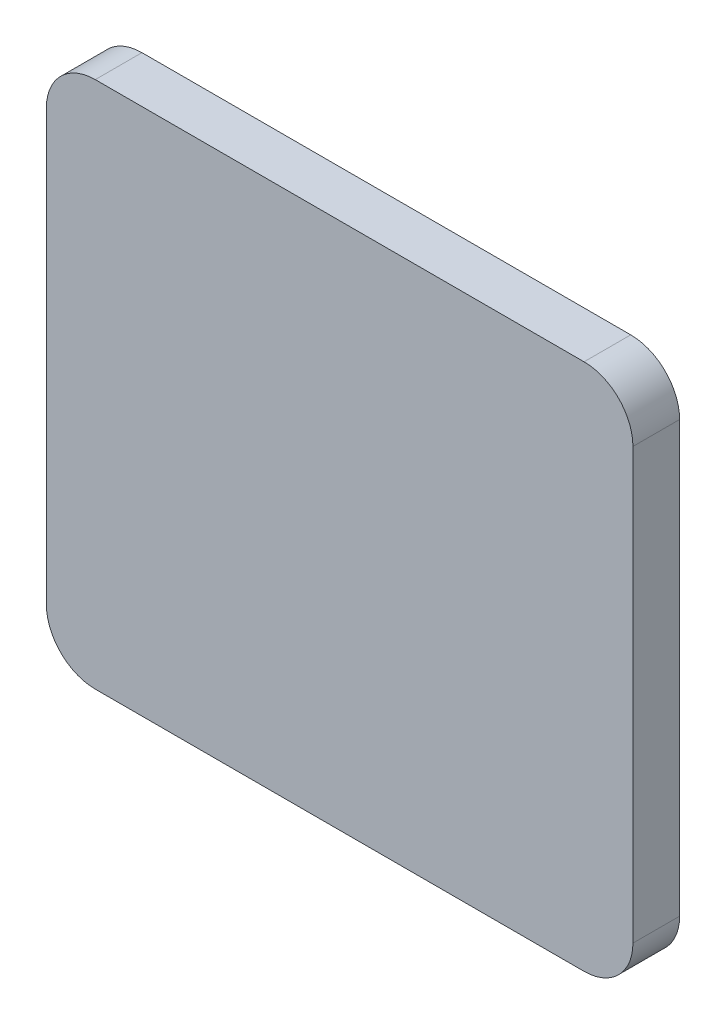
SolidWorks part; units mm, degrees
ref_plane "Front Plane" through (0, 0, 0) normal (0, 0, 1) x (1, 0, 0)
ref_plane "Top Plane" through (0, 0, 0) normal (0, 1, 0) x (1, 0, 0)
ref_plane "Right Plane" through (0, 0, 0) normal (1, 0, 0) x (0, 0, -1)
sketch "Sketch1" plane through (0, 0, 0) normal (0, 0, 1) x (1, 0, 0)
  line L0 (0, 5) -> (0, 49)
  line L1 (5, 0) -> (55, 0)
  line L2 (5, 54) -> (55, 54)
  line L3 (60, 49) -> (60, 5)
  arc A0 (0, 49) -> (5, 54) centre (5, 49) cw
  arc A1 (0, 5) -> (5, 0) centre (5, 5) ccw
  arc A2 (55, 0) -> (60, 5) centre (55, 5) ccw
  arc A3 (55, 54) -> (60, 49) centre (55, 49) cw
  point P7 (0, 54)
  point P10 (0, 0)
  point P13 (60, 0)
  dimension "D3" = 5
  dimension "D4" = 5
  dimension "D1" = 54
  dimension "D2" = 60
extrude "Boss-Extrude1" add sketch "Sketch1" along normal blind 4.7752
sketch "Sketch2" plane through (0, 0, 4.7752) normal (0, 0, 1) x (1, 0, 0)
  line L0 (183.0186, 521.1891) -> (865.6852, 521.1891) construction
  line L1 (183.4721, 529.4822) -> (866.1387, 529.4822) construction
  line L2 (181.2439, 528.0548) -> (863.9106, 528.0548) construction
  line L7 (19.8691, 28.8438) -> (19.2881, 28.3572)
  line L8 (19.2881, 28.3572) -> (18.8822, 27.9078)
  line L9 (18.8822, 27.9078) -> (18.3075, 27.2715)
  line L10 (18.3075, 27.2715) -> (17.8606, 26.7766)
  line L11 (17.8606, 26.7766) -> (17.5763, 26.4618)
  line L12 (17.5763, 26.4618) -> (17.4224, 26.2372)
  line L13 (17.4224, 26.2372) -> (17.2492, 25.9065)
  line L14 (17.2492, 25.9065) -> (17.2492, 25.6606)
  line L15 (17.2492, 25.6606) -> (17.2492, 25.3807)
  line L16 (17.2492, 25.3807) -> (17.4224, 24.2786)
  line L17 (17.4224, 24.2786) -> (17.6828, 23.5807)
  line L18 (17.6828, 23.5807) -> (17.8362, 23.1695)
  line L19 (17.8362, 23.1695) -> (17.9803, 22.7832)
  line L20 (17.9803, 22.7832) -> (18.1007, 22.4604)
  line L21 (18.1007, 22.4604) -> (18.2144, 22.1557)
  line L22 (18.4085, 20.4831) -> (17.7442, 19.7163)
  line L23 (21.1826, 20.9352) -> (21.7477, 18.6362)
  line L24 (30.0623, 41.0301) -> (30.3939, 40.8005)
  line L25 (30.3939, 40.8005) -> (30.5707, 40.8005)
  line L26 (30.5707, 40.8005) -> (30.7622, 40.9153)
  line L27 (38.1812, 40.4733) -> (38.4921, 39.9546)
  line L28 (38.0447, 39.328) -> (38.0816, 39.0467)
  line L29 (36.2955, 38.0196) -> (36.6942, 37.6823)
  line L30 (37.0925, 36.8802) -> (37.8941, 35.8611)
  line L31 (38.6385, 35.2424) -> (39.1212, 35.283)
  line L32 (39.1212, 35.283) -> (40.0166, 36.0841)
  line L33 (40.0166, 36.0841) -> (40.7211, 36.9169)
  line L34 (42.8215, 41.0301) -> (43.2748, 41.9093)
  line L35 (43.2748, 41.9093) -> (43.1854, 41.9728)
  line L36 (43.1854, 41.9728) -> (44.4975, 43.2915)
  line L37 (44.4975, 43.2915) -> (44.3554, 42.3659)
  line L38 (44.3554, 42.3659) -> (44.2137, 41.4319)
  line L39 (44.2137, 41.4319) -> (44.1203, 41.4319)
  line L40 (44.1203, 41.4319) -> (43.5539, 40.2139)
  line L41 (43.21, 37.2316) -> (43.21, 36.9573)
  line L42 (43.257, 36.7903) -> (43.257, 36.4775)
  line L43 (42.7089, 35.7793) -> (42.7089, 35.2023)
  line L44 (40.0908, 30.5826) -> (40.0908, 28.8438)
  line L45 (40.0908, 28.8438) -> (40.0908, 28.3572)
  line L46 (40.0908, 28.3572) -> (42.0558, 26.1361)
  line L47 (42.0558, 26.1361) -> (42.3352, 25.8202)
  line L48 (42.6677, 24.2006) -> (42.9387, 23.1123)
  line L49 (42.9387, 23.1123) -> (43.3368, 21.4956)
  line L50 (43.6062, 21.3545) -> (43.8552, 20.5895)
  line L51 (44.1203, 20.0346) -> (44.8963, 19.3792)
  line L52 (46.2642, 17.9578) -> (45.8969, 17.9578)
  line L53 (40.5893, 21.6092) -> (41.249, 20.5895)
  line L54 (41.2881, 20.2047) -> (41.5991, 19.5764)
  line L55 (30.188, 37.6446) -> (30.9361, 37.2066)
  line L56 (39.8628, 35.283) -> (40.0908, 30.5826)
  line L57 (39.4926, 24.7928) -> (39.3341, 24.4294)
  line L58 (39.3341, 24.4294) -> (38.0631, 22.1946)
  line L59 (33.1417, 18.0204) -> (30.2458, 17.0656)
  line L60 (20.8186, 34.4764) -> (20.8186, 28.3572)
  line L61 (30.188, 37.6446) -> (29.1962, 37.1114)
  line L62 (21.1943, 25.3237) -> (21.1943, 25.0948)
  line L63 (30.7622, 38.7051) -> (31.0642, 38.5253)
  line L64 (32.0076, 38.5673) -> (32.3932, 38.7559)
  line L65 (30.9679, 37.2044) -> (30.9774, 37.1857)
  line L66 (29.5571, 35.4668) -> (29.5571, 30.5826)
  line L67 (21.8901, 33.4938) -> (21.8901, 27.498)
  line L68 (24.1235, 22.3264) -> (24.5573, 21.9598)
  line L69 (29.5571, 18.4892) -> (29.5571, 25.0948)
  line L70 (30.7622, 35.8611) -> (30.7622, 30.5407)
  line L71 (30.5705, 25.0948) -> (30.5331, 18.4892)
  line L72 (38.2474, 33.9415) -> (38.2474, 27.9078)
  line L73 (36.4984, 22.9875) -> (35.2616, 21.7508)
  line L74 (35.2616, 21.7508) -> (34.2289, 20.9352)
  line L75 (27.5438, 34.1253) -> (28.1251, 32.9236)
  line L76 (27.5438, 34.1253) -> (26.4478, 33.7659)
  line L77 (26.4478, 33.7659) -> (26.5449, 32.6671)
  line L78 (24.8545, 33.1855) -> (25.8453, 32.2989)
  line L79 (24.8545, 33.1855) -> (23.9227, 32.2537)
  line L80 (23.9227, 32.2537) -> (24.7062, 31.3206)
  line L81 (22.7755, 30.7888) -> (22.4877, 29.7241)
  line L82 (22.7755, 30.7888) -> (24.0761, 30.4374)
  line L83 (22.4877, 29.7241) -> (23.4562, 28.9587)
  line L84 (22.2028, 27.6434) -> (23.4562, 27.9078)
  line L85 (22.2028, 27.6434) -> (22.4877, 26.2925)
  line L86 (22.4877, 26.2925) -> (23.648, 26.2925)
  line L87 (24.0761, 25.3237) -> (23.1741, 24.4217)
  line L88 (23.1741, 24.4217) -> (23.9227, 23.45)
  line L89 (23.9227, 23.45) -> (24.9587, 23.9358)
  line L90 (25.8453, 23.2567) -> (25.4702, 22.1203)
  line L91 (25.4702, 22.1203) -> (26.5449, 21.553)
  line L92 (26.5449, 21.553) -> (27.2111, 22.5111)
  line L93 (28.1251, 22.3264) -> (28.2487, 20.9976)
  line L94 (28.2487, 20.9976) -> (29.5571, 20.9976)
  line L95 (31.6904, 33.2973) -> (31.6904, 30.1094)
  line L96 (32.0076, 33.3499) -> (32.0076, 32.2589)
  line L97 (32.0076, 32.2589) -> (32.584, 32.8352)
  line L98 (32.584, 32.8352) -> (32.584, 35.1926)
  line L99 (33.0317, 35.0493) -> (33.0317, 32.6671)
  line L100 (33.0317, 32.6671) -> (32.0645, 31.7)
  line L101 (32.0645, 31.7) -> (32.0645, 29.7892)
  line L102 (33.1879, 31.1763) -> (32.0645, 29.7892)
  line L103 (33.1879, 31.1763) -> (33.1879, 32.2989)
  line L104 (33.1879, 32.2989) -> (34.0895, 33.2005)
  line L105 (34.0895, 33.2005) -> (34.0895, 33.7874)
  line L106 (34.5013, 33.8294) -> (34.5013, 33.0673)
  line L107 (34.5013, 33.0673) -> (33.5408, 32.2989)
  line L108 (33.5408, 32.2989) -> (33.5408, 31.3849)
  line L109 (33.5408, 31.3849) -> (35.5058, 33.3499)
  line L110 (35.5058, 33.3499) -> (35.5058, 34.3979)
  line L111 (36.0281, 34.2899) -> (35.9173, 33.0657)
  line L112 (35.9173, 33.0657) -> (32.2474, 29.5828)
  line L113 (34.2534, 29.7892) -> (32.584, 29.9022)
  line L114 (34.2534, 29.7892) -> (36.0368, 31.579)
  line L115 (36.2521, 31.359) -> (34.5013, 29.5908)
  line L116 (34.5013, 29.5908) -> (32.4324, 29.3228)
  line L117 (34.8915, 28.6876) -> (32.76, 28.5787)
  line L118 (34.8915, 28.6876) -> (38.2474, 32.2989)
  line L119 (38.2474, 31.6593) -> (35.1611, 28.3572)
  line L120 (35.1611, 28.3572) -> (32.8456, 28.1214)
  line L121 (32.8583, 27.7406) -> (35.7608, 27.7406)
  line L122 (35.7608, 27.7406) -> (36.1431, 27.3583)
  line L123 (36.1431, 27.3583) -> (37.5685, 28.3572)
  line L124 (37.5685, 28.3572) -> (37.5685, 29.1299)
  line L125 (37.8941, 29.1299) -> (37.8941, 28.1214)
  line L126 (37.8941, 28.1214) -> (36.4984, 26.9892)
  line L127 (36.4984, 26.9892) -> (36.8796, 26.5192)
  line L128 (36.8796, 26.5192) -> (37.2321, 26.5192)
  line L129 (37.1942, 26.1361) -> (36.8048, 26.1361)
  line L130 (36.8048, 26.1361) -> (35.5486, 27.1749)
  line L131 (35.5486, 27.1749) -> (32.7798, 27.1749)
  line L132 (32.49, 26.4506) -> (35.2616, 26.4506)
  line L133 (35.2616, 26.4506) -> (36.2521, 25.3599)
  line L134 (35.1611, 26.0597) -> (32.219, 26.0597)
  line L135 (35.1611, 26.0597) -> (36.0446, 25.1543)
  line L136 (34.2534, 25.4692) -> (31.542, 25.4692)
  line L137 (34.0895, 25.1543) -> (31.0642, 25.2326)
  line L138 (34.2534, 25.4692) -> (36.6004, 23.1222)
  line L139 (34.0895, 25.1543) -> (36.3773, 22.8665)
  line L140 (30.9679, 23.6364) -> (30.9679, 25.2351)
  line L141 (31.2189, 25.2286) -> (31.2189, 21.553)
  line L142 (30.9679, 23.5807) -> (30.9679, 21.4914)
  line L143 (30.9679, 21.4914) -> (31.4625, 20.7541)
  line L144 (31.4625, 20.7541) -> (31.4625, 20.1354)
  line L145 (31.2189, 21.553) -> (31.6689, 20.8347)
  line L146 (31.6689, 20.8347) -> (31.6689, 20.1236)
  line L147 (32.0645, 25.2067) -> (32.0645, 22.732)
  line L148 (32.0645, 22.732) -> (33.1856, 21.7508)
  line L149 (32.3932, 25.1982) -> (32.3932, 23.1222)
  line L150 (32.3932, 23.1222) -> (33.4953, 22.0177)
  line L151 (33.8798, 23.45) -> (34.7366, 22.734)
  line L152 (33.6942, 23.2266) -> (34.5192, 22.5111)
  line L153 (15.482, 10.3239) -> (47.6498, 10.3239) construction
  line L154 (15.6398, 46.289) -> (44.7901, 46.289)
  line L155 (49.7901, 41.289) -> (49.7901, 12.465)
  line L156 (44.7901, 7.465) -> (15.6398, 7.465)
  line L157 (10.6398, 12.465) -> (10.6398, 41.289)
  line L158 (16.32, 18.2559) -> (21.7621, 18.2237)
  line L159 (41.3569, 18.0204) -> (45.8969, 17.9578)
  arc A0 (20.8186, 34.4764) -> (29.1962, 37.1114) centre (18.9471, 55.0612) ccw
  arc A1 (21.1943, 25.0948) -> (30.2458, 17.0656) centre (33.0317, 29.3228) ccw
  arc A2 (33.1417, 18.0204) -> (34.8764, 19.2218) centre (2.1137, 64.6767) ccw
  arc A3 (29.8493, 39.3836) -> (30.7622, 38.7051) centre (30.8517, 39.779) ccw
  arc A4 (31.0642, 38.5253) -> (32.0076, 38.5673) centre (31.4803, 39.7949) ccw
  arc A5 (32.8912, 39.1874) -> (33.3315, 40.0392) centre (32.2474, 40.0599) ccw
  arc A6 (33.6942, 39.5117) -> (33.1879, 38.7051) centre (33.9698, 38.7765) ccw
  arc A7 (32.9406, 38.6569) -> (30.9679, 37.2044) centre (34.8915, 33.9415) ccw
  arc A8 (21.8901, 33.4938) -> (29.5571, 35.4668) centre (14.2088, 79.2252) ccw
  arc A9 (21.8901, 27.498) -> (22.9072, 24.0299) centre (28.8048, 27.6427) ccw
  arc A10 (24.5573, 21.9598) -> (29.5571, 18.4892) centre (35.9173, 32.9888) ccw
  arc A11 (29.5571, 30.5826) -> (29.5571, 25.0948) centre (30.8195, 27.8387) ccw
  arc A12 (30.7622, 30.5407) -> (30.5705, 25.0948) centre (30.071, 27.8387) cw
  arc A13 (30.7622, 35.8611) -> (38.2474, 33.9415) centre (41.6112, 62.6125) ccw
  arc A14 (38.2474, 27.9078) -> (36.4984, 22.9875) centre (29.8722, 28.1139) cw
  arc A15 (30.5331, 18.4892) -> (34.2289, 20.9352) centre (-10.6731, 84.7636) ccw
  arc A16 (28.1251, 32.9236) -> (29.5571, 33.0501) centre (29.0679, 30.4203) cw
  arc A17 (25.8453, 32.2989) -> (26.5449, 32.6671) centre (27.5357, 29.936) cw
  arc A18 (24.7062, 31.3206) -> (24.0761, 30.4374) centre (26.4182, 29.433) ccw
  arc A19 (23.4562, 28.9587) -> (23.4562, 27.9078) centre (26.2952, 28.4333) ccw
  arc A20 (23.648, 26.2925) -> (24.0761, 25.3237) centre (25.3101, 26.4479) ccw
  arc A21 (24.9587, 23.9358) -> (25.8453, 23.2567) centre (26.9731, 25.6472) ccw
  arc A22 (27.2111, 22.5111) -> (28.1251, 22.3264) centre (28.0983, 24.5479) ccw
  circle A23 centre (31.8029, 33.7916) radius 0.4868
  circle A24 centre (31.8029, 33.7916) radius 0.1499
  circle A25 centre (34.2534, 34.2201) radius 0.4627
  circle A26 centre (34.2534, 34.2201) radius 0.2002
  circle A27 centre (37.1631, 33.4938) radius 0.4965
  circle A28 centre (37.1631, 33.4938) radius 0.1818
  circle A29 centre (36.5449, 31.8608) radius 0.581
  circle A30 centre (36.5449, 31.8608) radius 0.2228
  circle A31 centre (37.7426, 29.433) radius 0.359
  circle A32 centre (37.7426, 29.433) radius 0.164
  circle A33 centre (37.5685, 26.2925) radius 0.4057
  circle A34 centre (37.5685, 26.2925) radius 0.1581
  circle A35 centre (36.4984, 24.9039) radius 0.5183
  circle A36 centre (36.4984, 24.9039) radius 0.1909
  circle A37 centre (31.542, 19.7163) radius 0.4265
  circle A38 centre (31.542, 19.7163) radius 0.1649
  circle A39 centre (33.6259, 21.553) radius 0.4827
  circle A40 centre (33.6259, 21.553) radius 0.2231
  circle A41 centre (33.4953, 23.5807) radius 0.4061
  circle A42 centre (34.8764, 22.3802) radius 0.3805
  circle A43 centre (33.4953, 23.5807) radius 0.142
  circle A44 centre (34.8764, 22.3802) radius 0.1953
  arc A45 (15.6398, 7.465) -> (10.6398, 12.465) centre (15.6398, 12.465) cw
  arc A46 (49.7901, 12.465) -> (44.7901, 7.465) centre (44.7901, 12.465) cw
  arc A47 (44.7901, 46.289) -> (49.7901, 41.289) centre (44.7901, 41.289) cw
  arc A48 (15.6398, 46.289) -> (10.6398, 41.289) centre (15.6398, 41.289) ccw
  spline S0 degree 3 poles (22.7379, 43.3112) (22.7387, 43.5151) (22.8735, 43.8364) (23.2896, 44.2347) (23.7368, 44.0067) (23.9157, 44.2829) (24.1257, 44.3158) (24.2472, 44.4838) (24.4161, 44.5147) (24.5617, 44.565) (24.7384, 44.6035) (24.9592, 44.6143) (25.1526, 44.6158) (25.3154, 44.6078) (25.3626, 44.5093) (25.468, 44.4462) (25.5814, 44.5219) (25.7205, 44.5468) (25.8713, 44.5487) (26.0272, 44.5146) (26.1854, 44.5161) (26.2762, 44.4164) (26.3599, 44.3502) (26.4391, 44.3118) (26.5083, 44.2565) (26.532, 44.2025) (26.5417, 44.1294) (26.6597, 44.1865) (26.7624, 44.1998) (26.8986, 44.1721) (27.0389, 44.1391) (27.1296, 44.0426) (27.2172, 43.9689) (27.275, 43.8864) (27.3569, 43.8241) (27.4096, 43.7413) (27.4677, 43.7058) (27.5158, 43.6513) (27.545, 43.587) (27.6196, 43.576) (27.6586, 43.5123) (27.7401, 43.4656) (27.8067, 43.3833) (27.8873, 43.3201) (27.9295, 43.2334) (27.9437, 43.162) (27.9742, 43.1109) (28.0189, 43.0863) (28.0527, 43.029) (28.0524, 42.9616) (28.0354, 42.8865) (28.0475, 42.8342) (28.0417, 42.8007) knots 0 0 0 0 0.086351 0.154058 0.220973 0.248992 0.281446 0.30751 0.333439 0.353116 0.375297 0.412158 0.447968 0.464426 0.475171 0.493298 0.509401 0.529744 0.555188 0.574247 0.600124 0.619551 0.630296 0.646781 0.658128 0.66741 0.67337 0.684834 0.707763 0.72496 0.743737 0.769731 0.780611 0.793782 0.81328 0.824958 0.83589 0.842275 0.856942 0.863148 0.872897 0.887224 0.903722 0.918673 0.931303 0.944718 0.950454 0.9565 0.966505 0.977653 0.985152 1 1 1 1
  spline S1 degree 3 poles (28.0417, 42.8007) (28.0545, 42.7771) (28.0906, 42.7508) (28.1403, 42.7168) (28.1732, 42.6769) (28.2117, 42.6308) (28.2397, 42.5796) (28.2756, 42.5336) (28.3201, 42.5159) (28.3575, 42.4142) (28.3794, 42.2742) (28.3805, 42.0844) (28.3725, 41.946) (28.3797, 41.8406) (28.3785, 41.7689) (28.3783, 41.7137) (28.3793, 41.6581) (28.369, 41.6177) (28.3589, 41.5568) (28.3486, 41.5139) (28.318, 41.4735) (28.3371, 41.4194) (28.2798, 41.3698) (28.2659, 41.2989) (28.2514, 41.235) (28.208, 41.1915) (28.1911, 41.1332) (28.1683, 41.0817) (28.1555, 41.0282) (28.1567, 40.9685) (28.1459, 40.9011) (28.1483, 40.8411) (28.148, 40.7646) (28.1473, 40.6711) (28.1422, 40.5382) (28.0971, 40.4381) (28.0752, 40.3387) (28.0367, 40.2553) (28.0161, 40.1367) (27.9385, 40.0605) (27.8807, 39.9779) (27.8159, 39.927) (27.7361, 39.863) (27.6813, 39.7888) (27.5931, 39.7554) (27.5367, 39.697) (27.5107, 39.6238) (27.4623, 39.5637) (27.4431, 39.4888) (27.4242, 39.3852) (27.3305, 39.3541) (27.3082, 39.2859) (27.2623, 39.2732) (27.269, 39.2294) (27.2871, 39.1888) (27.3531, 39.1962) (27.4252, 39.1445) (27.5145, 39.0767) (27.4946, 38.9773) (27.5414, 38.903) (27.6165, 38.8484) (27.6086, 38.7695) (27.5957, 38.7008) (27.6508, 38.6594) (27.7278, 38.6091) (27.8562, 38.617) (28.0022, 38.6206) (28.1304, 38.561) (28.2559, 38.5143) (28.3598, 38.4293) (28.4653, 38.3979) (28.5444, 38.3255) (28.641, 38.2679) (28.7204, 38.173) (28.7883, 38.0619) (28.8918, 37.9905) (29.0033, 37.9179) (29.1177, 37.855) (29.1841, 37.7521) (29.2795, 37.6623) (29.4439, 37.6187) (29.5024, 37.4829) (29.5571, 37.4352) knots 0 0 0 0 0.010852 0.018706 0.025148 0.032477 0.043899 0.049665 0.056707 0.062596 0.093099 0.117124 0.141963 0.151336 0.161515 0.172101 0.174543 0.184851 0.189403 0.200606 0.20298 0.210035 0.220845 0.230705 0.240246 0.247689 0.255658 0.26531 0.271491 0.278539 0.290315 0.300037 0.303724 0.322485 0.339513 0.358966 0.367957 0.382208 0.397504 0.417168 0.426219 0.439876 0.451385 0.469487 0.476935 0.490481 0.501887 0.509309 0.522395 0.534336 0.550695 0.55757 0.562552 0.567058 0.573713 0.578814 0.591897 0.610993 0.618878 0.631544 0.645974 0.65386 0.663435 0.672908 0.679748 0.7024 0.723544 0.740908 0.76084 0.779696 0.796519 0.805879 0.824355 0.843443 0.857193 0.878731 0.895052 0.913658 0.932386 0.945629 0.968012 1 1 1 1
  spline S2 degree 3 poles (22.7379, 43.3112) (22.628, 43.4178) (22.6155, 43.2011) (22.4543, 43.2529) (22.4044, 43.1262) (22.2951, 43.0519) (22.3311, 42.8685) (22.2305, 42.8771) (22.2499, 42.7429) (22.242, 42.6522) (22.2425, 42.5223) (22.2495, 42.3962) (22.2793, 42.2753) (22.3651, 42.1965) (22.4583, 42.1456) (22.5665, 42.088) (22.6714, 42.0259) (22.6951, 41.8915) (22.6389, 41.7875) (22.614, 41.6739) (22.6059, 41.5777) (22.5999, 41.4944) (22.6256, 41.405) (22.6294, 41.3029) (22.6706, 41.2092) (22.7028, 41.1217) (22.6878, 41.0168) (22.7382, 40.921) (22.7509, 40.809) (22.8549, 40.7895) (22.8361, 40.7167) (22.8308, 40.6632) (22.7953, 40.5905) (22.6737, 40.5472) (22.6907, 40.3797) (22.5917, 40.2734) (22.5951, 40.1412) (22.659, 40.0396) (22.6965, 39.9427) (22.7514, 39.8561) (22.7534, 39.7685) (22.7962, 39.6848) (22.8397, 39.6135) (22.9181, 39.5832) (22.9447, 39.5065) (22.9362, 39.4038) (22.9296, 39.2965) (22.9548, 39.1889) (22.9819, 39.112) (23.0039, 39.0305) (23.0508, 38.9443) (23.0533, 38.8583) (23.0808, 38.7909) (23.1121, 38.7543) (23.1323, 38.7109) (23.1523, 38.67) (23.1644, 38.6286) (23.2208, 38.6167) (23.2264, 38.5488) (23.2786, 38.51) (23.3028, 38.4585) (23.3392, 38.4171) (23.3834, 38.3867) (23.4144, 38.3344) (23.4459, 38.2864) (23.467, 38.2439) (23.4932, 38.2022) (23.4388, 38.1817) (23.3828, 38.1992) (23.3151, 38.2099) (23.2445, 38.2085) (23.181, 38.2061) (23.1168, 38.2149) (23.0575, 38.1951) (22.9882, 38.178) (22.9194, 38.1541) (22.8599, 38.1321) (22.8144, 38.121) (22.7614, 38.0979) (22.7146, 38.0498) (22.646, 38.0272) (22.6031, 37.9818) (22.5499, 37.9495) (22.4687, 37.9182) (22.4011, 37.8521) (22.3266, 37.8165) (22.2652, 37.7826) (22.2048, 37.7481) (22.1314, 37.7069) (22.0664, 37.647) (21.9717, 37.6116) (21.895, 37.5482) (21.828, 37.4787) (21.726, 37.4267) (21.6375, 37.3567) (21.5709, 37.2629) (21.507, 37.2132) (21.3683, 37.1308) (21.2186, 37.2618) (21.1356, 37.1624) knots 0 0 0 0 0.027086 0.034693 0.048131 0.064249 0.083207 0.084475 0.096796 0.111976 0.123411 0.139893 0.156828 0.163933 0.179591 0.193308 0.207128 0.219196 0.236068 0.247092 0.259227 0.26962 0.275564 0.291229 0.304419 0.310783 0.323221 0.339315 0.34786 0.359444 0.36414 0.370883 0.378849 0.390518 0.410272 0.426453 0.438466 0.452752 0.467513 0.474478 0.487783 0.496434 0.50694 0.515788 0.523497 0.532852 0.551647 0.560194 0.570925 0.579873 0.589357 0.604421 0.60882 0.614281 0.620915 0.625183 0.630408 0.634357 0.642773 0.649653 0.656179 0.66212 0.668604 0.674399 0.683003 0.687887 0.692388 0.695701 0.703925 0.713381 0.719033 0.72839 0.73541 0.741036 0.749738 0.760217 0.766196 0.771685 0.776396 0.786027 0.794347 0.800643 0.807289 0.815752 0.830541 0.839217 0.844241 0.854836 0.863293 0.873318 0.885069 0.897708 0.907438 0.918279 0.937015 0.945846 0.957808 0.96498 1 1 1 1
  spline S3 degree 3 poles (21.1356, 37.1624) (21.0628, 37.1644) (20.9719, 37.0597) (20.8439, 37.0944) (20.7758, 37.0657) (20.7164, 37.0336) (20.6415, 36.9991) (20.5652, 36.9914) (20.5002, 36.9812) (20.4218, 36.9484) (20.3253, 36.9224) (20.2262, 36.8777) (20.1384, 36.8622) (20.0734, 36.8388) (20.0116, 36.8162) (19.9533, 36.8093) (19.8725, 36.8117) (19.7917, 36.8053) (19.7588, 36.8624) (19.7245, 36.8752) (19.6983, 36.9065) (19.6727, 36.9393) (19.6354, 36.9642) (19.6185, 37.001) (19.5965, 37.032) (19.549, 37.079) (19.5274, 37.1728) (19.4607, 37.159) (19.4426, 37.1839) (19.3973, 37.222) (19.3684, 37.3005) (19.285, 37.334) (19.2229, 37.3518) (19.1639, 37.4111) (19.1141, 37.474) (19.0666, 37.5184) (19.0568, 37.5411) knots 0 0 0 0 0.088725 0.135223 0.148032 0.178202 0.218568 0.247404 0.271809 0.298835 0.350984 0.394148 0.431235 0.459679 0.478642 0.511929 0.529919 0.580492 0.5922 0.606343 0.623304 0.641357 0.657293 0.676839 0.689736 0.703557 0.760843 0.768339 0.778535 0.79436 0.843176 0.869999 0.9009 0.92107 0.970613 1 1 1 1
  spline S4 degree 3 poles (19.0568, 37.5411) (18.0375, 37.8774) (18.8583, 38.8443) (17.9845, 39.4967) (18.2192, 39.8232) (18.2627, 40.0843) (18.4062, 40.5206) (18.8182, 40.291) (19.0631, 40.4984) (19.4748, 40.5707) (19.7826, 40.7665) (19.8973, 41.0301) knots 0 0 0 0 0.376708 0.467988 0.509995 0.595137 0.648251 0.745711 0.786301 0.836117 1 1 1 1
  spline S5 degree 3 poles (19.8973, 41.0301) (20.4772, 41.3579) (20.6557, 43.1208) (19.4838, 43.1967) (19.2914, 42.7608) (19.1222, 42.4506) (18.8659, 42.1995) (18.6262, 42.2843) (18.3853, 42.2216) (18.2957, 42.4133) (18.0323, 42.6242) (17.9983, 43.0004) (18.2741, 43.1367) knots 0 0 0 0 0.438636 0.496705 0.586833 0.670292 0.712643 0.772203 0.802779 0.837393 0.873852 1 1 1 1
  spline S6 degree 2 poles (18.2741, 43.1367) (18.6516, 43.5246) (18.8165, 44.0212) knots 0 0 0 1 1 1
  spline S7 degree 3 poles (18.8165, 44.0212) (18.8048, 44.1205) (18.6904, 44.1542) (18.5709, 44.2698) (18.4749, 44.2485) (18.3576, 44.2514) (18.25, 44.2498) (18.1005, 44.2501) (17.9685, 44.25) (17.8203, 44.2502) (17.7098, 44.2495) (17.5755, 44.2516) (17.4409, 44.2278) (17.3407, 44.1127) (17.2326, 44.1401) (17.1633, 44.0736) (17.0826, 44.0088) (16.9921, 43.9815) (16.9094, 43.9312) (16.8509, 43.8772) (16.8349, 43.7898) (16.7632, 43.7529) (16.6584, 43.6447) (16.6206, 43.5227) (16.5382, 43.4638) knots 0 0 0 0 0.08881 0.128786 0.173447 0.188621 0.260728 0.293026 0.355603 0.408086 0.458551 0.478737 0.55845 0.603744 0.629986 0.670398 0.700602 0.747048 0.773005 0.80926 0.831376 0.866647 0.891632 1 1 1 1
  spline S8 degree 3 poles (16.5382, 43.4638) (16.4857, 43.4046) (16.4491, 43.287) (16.3572, 43.124) (16.3369, 43.0146) (16.32, 42.9537) knots 0 0 0 0 0.410471 0.659075 1 1 1 1
  spline S9 degree 3 poles (16.32, 42.9537) (16.2906, 42.7595) (16.3027, 42.5152) (16.2942, 42.2092) (16.3656, 42.0857) (16.4443, 42.0145) (16.452, 41.8862) (16.5494, 41.7838) (16.5704, 41.614) (16.7709, 41.5026) (16.6429, 41.3361) (16.4492, 40.9917) (16.5316, 40.3472) (16.0781, 40.2747) (15.9303, 40.1872) (15.8614, 40.0566) (15.8253, 39.9127) (15.8544, 39.7453) (15.7042, 39.6972) (15.618, 39.6407) (15.5935, 39.566) (15.5503, 39.5022) (15.5657, 39.382) (15.5395, 39.2908) (15.5572, 39.2356) knots 0 0 0 0 0.130856 0.182579 0.206917 0.229293 0.254239 0.291682 0.323038 0.371253 0.411275 0.440832 0.664404 0.712155 0.74233 0.782825 0.81048 0.849624 0.880749 0.907653 0.919008 0.93502 0.960224 1 1 1 1
  spline S10 degree 3 poles (15.5572, 39.2356) (15.4601, 39.2444) (15.4456, 39.1291) (15.356, 39.0385) (15.3007, 38.923) (15.3519, 38.7529) (15.1831, 38.6795) (15.1157, 38.5562) (15.0791, 38.4046) (15.1104, 38.2372) (15.1401, 38.0688) (15.2375, 37.992) (15.295, 37.9338) (15.2764, 37.8281) (15.2212, 37.7197) (15.0877, 37.4456) (14.8931, 37.0962) (14.7062, 36.5953) (14.3968, 36.5732) (14.3275, 36.5114) knots 0 0 0 0 0.061603 0.089473 0.114441 0.175549 0.215939 0.259079 0.299817 0.35411 0.413777 0.443482 0.466697 0.480594 0.53555 0.578195 0.754787 0.914954 1 1 1 1
  spline S11 degree 3 poles (14.3275, 36.5114) (14.1275, 36.3089) (13.7759, 35.9886) (13.6383, 35.4179) (13.5694, 35.031) (13.6733, 34.6917) (13.8196, 34.4396) (13.9587, 34.1966) (14.1634, 34.1332) (14.3517, 34.1409) (14.4284, 34.3025) (14.5518, 34.4546) (14.6362, 34.6715) (14.706, 34.8964) (14.8376, 35.0452) (14.8759, 35.2493) (15.071, 35.2676) (15.2454, 35.2547) (15.3238, 35.0881) (15.2862, 34.9057) (15.2097, 34.7022) (15.0973, 34.436) (14.9582, 34.1893) (14.9496, 33.9318) (15.052, 33.7803) (15.2474, 33.6954) (15.4764, 33.7464) (15.8244, 33.8309) (16.2177, 34.1123) (16.5551, 34.5457) (16.6396, 35.0268) (16.7472, 35.5251) (16.2458, 35.8691) (16.4653, 36.116) (16.5747, 36.3215) (16.6908, 36.5084) (16.7739, 37.0252) (16.9312, 36.7661) (17.0333, 36.5522) (17.2952, 36.2055) (17.5726, 35.7941) (17.9484, 35.2712) (18.5543, 34.558) (19.0464, 33.9601) (19.4647, 33.6794) (19.4852, 33.6622) (19.5261, 33.6479) (19.5713, 33.6545) (19.6425, 33.653) (19.7258, 33.6563) (19.8359, 33.6511) (19.9569, 33.6777) (20.1169, 33.7216) (20.2101, 33.783) (20.3256, 33.7961) (20.3172, 33.758) (20.3219, 33.7101) (20.3186, 33.6166) (20.3203, 33.475) (20.3197, 33.3255) (20.3198, 33.1355) (20.3197, 32.9254) (20.3198, 32.6817) (20.3197, 32.4734) (20.3198, 32.2433) (20.3191, 31.7958) (20.3277, 31.0014) (20.2784, 29.9416) (20.3654, 29.0135) (19.8691, 28.8438) knots 0 0 0 0 0.043073 0.064146 0.08466 0.099287 0.114403 0.127922 0.137686 0.144556 0.152875 0.161107 0.173618 0.18626 0.194893 0.202361 0.213355 0.218589 0.22702 0.235576 0.245624 0.2586 0.277796 0.286125 0.294653 0.302686 0.315674 0.327566 0.354993 0.384162 0.4046 0.426182 0.454502 0.462424 0.469832 0.487877 0.505161 0.509096 0.525318 0.542966 0.570713 0.598282 0.636422 0.707577 0.708695 0.709799 0.711452 0.714799 0.716318 0.721843 0.726943 0.732264 0.739923 0.75011 0.751553 0.752654 0.754582 0.759126 0.76587 0.775408 0.780839 0.793557 0.806009 0.816342 0.823891 0.839535 0.88161 0.938555 1 1 1 1
  spline S12 degree 3 poles (18.2144, 22.1557) (18.1475, 22.0712) (17.9661, 21.8627) (18.117, 21.5491) (18.1351, 21.2984) (18.2878, 20.9608) (18.2847, 20.674) (18.4085, 20.4831) knots 0 0 0 0 0.203553 0.381302 0.536178 0.628864 1 1 1 1
  spline S13 degree 3 poles (17.7442, 19.7163) (17.4158, 19.6558) (17.0601, 19.5504) (16.5521, 19.3591) (16.491, 19.084) (16.3016, 18.9464) (16.3245, 18.7699) (16.3187, 18.6367) (16.3207, 18.4602) (16.3198, 18.3337) (16.32, 18.2559) knots 0 0 0 0 0.399127 0.520491 0.627122 0.73103 0.777993 0.839899 0.901805 1 1 1 1
  spline S14 degree 1 poles (21.1943, 25.0948) (20.7892, 24.8238) knots 0 0 1 1
  spline S15 degree 3 poles (20.7892, 24.8238) (20.325, 24.7055) (20.6392, 24.7498) (20.6799, 24.515) (20.7537, 24.348) (20.6705, 24.1437) (20.8281, 24.0176) (20.7751, 23.832) (20.7924, 23.6441) (20.7891, 23.4483) (20.7845, 23.1576) (20.8216, 22.9576) (20.7743, 22.6977) (20.9032, 22.7496) (20.9858, 22.7177) (21.1235, 22.6637) (21.0385, 22.5097) (21.1502, 22.4242) (21.1262, 22.2821) (21.1381, 22.1362) (21.135, 21.965) (21.1357, 21.8233) (21.1355, 21.7064) (21.1357, 21.619) (21.1352, 21.5511) (21.1381, 21.4669) (21.118, 21.3745) (21.1643, 21.2951) (21.2004, 21.2288) (21.2284, 21.1406) (21.2389, 21.0126) (21.1382, 20.982) (21.1826, 20.9352) knots 0 0 0 0 0.077438 0.106296 0.149847 0.203247 0.2286 0.271005 0.318122 0.360528 0.404504 0.512215 0.525438 0.546092 0.574323 0.595169 0.629726 0.656703 0.675161 0.72204 0.758569 0.791445 0.818842 0.838324 0.851109 0.865112 0.896262 0.911134 0.926259 0.947647 0.976205 1 1 1 1
  spline S16 degree 1 poles (21.7477, 18.6362) (21.7621, 18.2237) knots 0 0 1 1
  spline S17 degree 3 poles (30.7622, 40.9153) (31.0973, 41.2058) (31.0808, 41.639) (31.2189, 42.0115) knots 0 0 0 0 1 1 1 1
  spline S18 degree 3 poles (31.2189, 42.0115) (31.3555, 42.3153) (31.4152, 42.816) (31.8152, 43.1308) (31.9069, 43.3058) (32.1034, 43.3741) (32.2146, 43.4629) (32.3348, 43.5362) (32.4922, 43.5647) (32.6337, 43.6914) (32.7885, 43.6617) (32.9525, 43.6665) (33.1312, 43.6497) (33.3647, 43.7038) (33.5083, 43.5568) (33.6867, 43.4018) (33.8208, 43.5726) (33.9552, 43.6849) (34.1017, 43.7821) (34.223, 43.9034) (34.3511, 43.9818) (34.4899, 44.0113) (34.6309, 44.0784) (34.78, 44.1529) (34.9729, 44.1156) (35.142, 44.1852) (35.3343, 44.1634) (35.5325, 44.2029) (35.7726, 44.181) (35.9803, 44.218) (36.2259, 44.1793) (36.3825, 44.1629) (36.4984, 44.1426) knots 0 0 0 0 0.17615 0.189902 0.237186 0.261733 0.283936 0.303668 0.326685 0.357665 0.385206 0.395533 0.434549 0.47127 0.494473 0.529826 0.556898 0.578438 0.615056 0.637458 0.658571 0.684131 0.702913 0.7319 0.759129 0.79083 0.814168 0.848119 0.884377 0.92608 0.945237 1 1 1 1
  spline S19 degree 3 poles (36.4984, 44.1426) (36.6737, 44.0834) (36.9026, 44.027) (37.1511, 43.9156) (37.2364, 43.8448) (37.3214, 43.801) (37.4068, 43.7496) (37.481, 43.6585) (37.5657, 43.5675) (37.6788, 43.4998) (37.7632, 43.4168) (37.8612, 43.4024) (37.9488, 43.3836) (38.0442, 43.3436) (38.1449, 43.2893) (38.238, 43.245) (38.3169, 43.1812) (38.385, 43.1208) (38.4399, 43.0463) (38.5232, 42.9865) (38.59, 42.9188) (38.6624, 42.8464) (38.7124, 42.7598) (38.7849, 42.6628) (38.8169, 42.5463) (38.8668, 42.4509) (38.9262, 42.3493) (38.9479, 42.233) (38.9852, 42.117) (38.9922, 42.0135) (39.0035, 41.8968) (38.9821, 41.7256) (38.9835, 41.541) (38.894, 41.3856) (38.8236, 41.2797) (38.7291, 41.1887) (38.6281, 41.1) (38.5801, 40.9974) (38.4931, 40.9309) (38.4061, 40.8426) (38.296, 40.7399) (38.1798, 40.6112) (38.0495, 40.5829) (38.1812, 40.4733) knots 0 0 0 0 0.103422 0.132384 0.151303 0.16505 0.185981 0.206449 0.230462 0.255083 0.280519 0.293817 0.309453 0.330863 0.351386 0.373691 0.388264 0.408086 0.424614 0.439631 0.465119 0.477948 0.496724 0.520949 0.545116 0.563532 0.581255 0.610638 0.629045 0.649345 0.66848 0.694589 0.746121 0.768206 0.793828 0.817253 0.841506 0.868649 0.878345 0.902434 0.938151 0.962529 1 1 1 1
  spline S20 degree 3 poles (38.4921, 39.9546) (38.5667, 39.859) (38.5728, 39.6586) (38.3691, 39.4157) (38.1943, 39.3093) (38.0447, 39.328) knots 0 0 0 0 0.37541 0.553082 1 1 1 1
  spline S21 degree 3 poles (38.0816, 39.0467) (38.0984, 38.8806) (37.8512, 38.7595) (37.8562, 38.5599) (37.8631, 38.498) (37.8133, 38.4211) (37.7792, 38.3646) (37.7426, 38.3415) knots 0 0 0 0 0.617781 0.671882 0.745655 0.845399 1 1 1 1
  spline S22 degree 3 poles (37.7426, 38.3415) (37.6312, 38.2372) (37.4944, 37.8089) (37.1646, 37.8512) (37.0229, 37.8452) (36.8932, 37.8502) (36.7649, 37.8386) (36.6504, 37.886) (36.563, 37.9396) (36.4427, 38.0286) (36.3214, 38.0198) (36.2521, 38.0814) knots 0 0 0 0 0.374483 0.457079 0.53517 0.616012 0.67637 0.74954 0.819141 0.850564 1 1 1 1
  spline S23 degree 2 poles (36.2521, 38.0814) (36.1841, 38.0534) (36.2955, 38.0196) knots 0 0 0 1 1 1
  spline S24 degree 3 poles (36.6942, 37.6823) (36.7439, 37.6375) (36.7769, 37.5489) (36.7741, 37.4045) (36.7568, 37.3064) (36.7467, 37.1883) (36.8738, 37.0373) (37.0334, 37.0014) (37.0925, 36.8802) knots 0 0 0 0 0.200568 0.27522 0.443413 0.51125 0.629363 1 1 1 1
  spline S25 degree 3 poles (37.8941, 35.8611) (37.9811, 35.8659) (38.2391, 35.7608) (38.4445, 35.5705) (38.6791, 35.3975) (38.614, 35.2893) (38.6385, 35.2424) knots 0 0 0 0 0.238857 0.766773 0.838569 1 1 1 1
  spline S26 degree 3 poles (40.7211, 36.9169) (40.6942, 37.0553) (40.69, 37.3514) (40.6076, 37.7476) (40.7184, 38.1052) (40.8695, 38.365) (41.0265, 38.613) (41.2044, 38.9048) (41.4925, 38.7711) (41.6289, 38.9493) (41.7686, 39.1229) (41.6212, 39.2582) (41.5886, 39.376) (41.5882, 39.4973) (41.622, 39.6042) (41.6343, 39.7091) (41.6838, 39.787) (41.7169, 39.87) (41.7739, 39.9852) (41.8602, 40.0905) (41.9996, 40.2362) (42.144, 40.1502) (42.2069, 40.1872) knots 0 0 0 0 0.100189 0.215635 0.283048 0.365159 0.428958 0.50503 0.569769 0.597156 0.660607 0.694122 0.7234 0.747696 0.780271 0.803935 0.822499 0.845799 0.868484 0.914292 0.946785 1 1 1 1
  spline S27 degree 3 poles (42.2069, 40.1872) (42.2487, 40.3334) (42.3756, 40.5244) (42.7241, 40.6717) (42.7319, 40.9366) (42.8215, 41.0301) knots 0 0 0 0 0.417327 0.618734 1 1 1 1
  spline S28 degree 3 poles (43.5539, 40.2139) (43.6826, 40.0966) (43.7215, 39.8368) (43.393, 39.6063) (43.6073, 39.4343) (43.6499, 39.3836) knots 0 0 0 0 0.487889 0.699773 1 1 1 1
  spline S29 degree 3 poles (43.6499, 39.3836) (43.6771, 39.3287) (43.6612, 39.2371) (43.6805, 39.1202) (43.6433, 39.0383) (43.6303, 38.9416) (43.5962, 38.8722) (43.5812, 38.8297) knots 0 0 0 0 0.298243 0.489248 0.599969 0.761408 1 1 1 1
  spline S30 degree 3 poles (43.5812, 38.8297) (43.5278, 38.7657) (43.4442, 38.6788) (43.3096, 38.6046) (43.2101, 38.5716) (43.1113, 38.4892) (42.9769, 38.3618) (43.0909, 38.241) (43.1713, 38.1686) (43.2001, 38.0606) (43.2428, 37.9403) (43.228, 37.8195) (43.2318, 37.6947) (43.2243, 37.6142) (43.2374, 37.5273) (43.1811, 37.4951) (43.1622, 37.404) (43.2229, 37.3267) (43.2097, 37.2547) (43.21, 37.2316) knots 0 0 0 0 0.129508 0.181323 0.236554 0.286858 0.388212 0.450941 0.505653 0.55713 0.617533 0.701398 0.740214 0.809314 0.829379 0.86641 0.892588 0.963678 1 1 1 1
  spline S31 degree 3 poles (43.21, 36.9573) (43.1921, 36.9505) (43.161, 36.9169) (43.1914, 36.8687) (43.2286, 36.8407) (43.2557, 36.8085) (43.257, 36.7903) knots 0 0 0 0 0.312785 0.448309 0.745432 1 1 1 1
  spline S32 degree 3 poles (43.257, 36.4775) (43.19, 36.4106) (43.1902, 36.2338) (43.0322, 36.1413) (42.9346, 35.9959) (42.7963, 35.9657) (42.7214, 35.917) knots 0 0 0 0 0.354972 0.539017 0.647574 1 1 1 1
  spline S33 degree 2 poles (42.7214, 35.917) (42.7063, 35.849) (42.7089, 35.7793) knots 0 0 0 1 1 1
  spline S34 degree 3 poles (42.7089, 35.2023) (42.7985, 34.9531) (43.0152, 34.7546) (43.2133, 34.4403) (43.2368, 34.2789) (43.3226, 34.1103) (43.3643, 33.9394) (43.3562, 33.7803) (43.3719, 33.6506) (43.3673, 33.5134) (43.353, 33.3723) (43.3457, 33.2427) (43.3433, 33.1515) (43.3278, 33.0055) (43.307, 32.8845) (43.2853, 32.7954) knots 0 0 0 0 0.296728 0.336644 0.428047 0.480927 0.555664 0.628855 0.664903 0.706974 0.78781 0.829665 0.85755 0.893705 1 1 1 1
  spline S35 degree 3 poles (43.2853, 32.7954) (43.2973, 32.6127) (43.0903, 32.2362) (42.7596, 31.6249) (42.188, 31.2315) (41.7176, 30.8355) (41.0027, 30.644) (40.4728, 30.5007) (40.0908, 30.5826) knots 0 0 0 0 0.120883 0.305433 0.48332 0.606986 0.737261 1 1 1 1
  spline S36 degree 3 poles (42.3352, 25.8202) (42.4738, 25.7261) (42.4523, 25.5066) (42.4695, 25.2124) (42.4364, 24.99) (42.5061, 24.8299) (42.5362, 24.5681) (42.6399, 24.3719) (42.6677, 24.2006) knots 0 0 0 0 0.227051 0.384593 0.531271 0.615245 0.690599 1 1 1 1
  spline S37 degree 2 poles (43.3368, 21.4956) (43.5238, 21.5323) (43.6062, 21.3545) knots 0 0 0 1 1 1
  spline S38 degree 3 poles (43.8552, 20.5895) (44.114, 20.4796) (43.8116, 20.1384) (44.1203, 20.0346) knots 0 0 0 0 1 1 1 1
  spline S39 degree 3 poles (44.8963, 19.3792) (44.9905, 19.2897) (45.166, 19.3397) (45.3869, 19.3) (45.5409, 19.2487) (45.7003, 19.2298) (45.8423, 19.165) (45.9958, 19.0995) (46.1412, 18.9721) (46.2316, 18.7894) (46.3059, 18.6096) (46.2787, 18.4183) (46.3055, 18.2072) (46.2699, 18.0465) (46.2642, 17.9578) knots 0 0 0 0 0.14306 0.21155 0.281667 0.347428 0.411982 0.477139 0.557727 0.648474 0.733415 0.795865 0.887604 1 1 1 1
  spline S40 degree 3 poles (39.3341, 24.4294) (39.4579, 24.4632) (40.0251, 24.177) (39.8355, 23.8072) (39.8728, 23.5922) (39.8688, 23.2353) (40.0378, 22.9438) (40.044, 22.7113) knots 0 0 0 0 0.345201 0.48114 0.538844 0.661852 1 1 1 1
  spline S41 degree 3 poles (40.044, 22.7113) (40.097, 22.6044) (40.1334, 22.4506) (40.2446, 22.2949) (40.2695, 22.1974) (40.3413, 22.1149) (40.3486, 22.0147) (40.408, 21.9204) (40.4585, 21.7743) (40.5653, 21.6912) (40.5893, 21.6092) knots 0 0 0 0 0.292157 0.372162 0.460549 0.531422 0.629717 0.69196 0.800033 1 1 1 1
  spline S42 degree 3 poles (41.249, 20.5895) (41.2096, 20.4641) (41.209, 20.3163) (41.2881, 20.2047) knots 0 0 0 0 1 1 1 1
  spline S43 degree 3 poles (41.5991, 19.5764) (41.5457, 19.4434) (41.4989, 19.2401) (41.4505, 19.0369) (41.4436, 18.9709) knots 0 0 0 0 0.682775 1 1 1 1
  spline S44 degree 3 poles (41.4436, 18.9709) (41.4383, 18.8064) (41.3192, 18.5014) (41.3433, 18.1744) (41.3569, 18.0204) knots 0 0 0 0 0.510668 1 1 1 1
  spline S45 degree 2 poles (20.8186, 28.3572) (20.9301, 26.8319) (21.1943, 25.3237) knots 0 0 0 1 1 1
  spline S46 degree 3 poles (30.9361, 37.2066) (33.6766, 35.8117) (36.8363, 35.4317) (39.8628, 35.283) knots 0 0 0 0 1 1 1 1
  spline S47 degree 3 poles (40.0908, 28.3572) (40.0667, 28.1058) (40.1488, 27.7098) (40.0766, 27.1504) (40.0929, 26.7691) (40.0885, 26.3471) (40.0999, 26.0888) (40.044, 25.9065) knots 0 0 0 0 0.307117 0.48414 0.685338 0.772489 1 1 1 1
  spline S48 degree 3 poles (40.044, 25.9065) (39.9148, 25.5117) (39.6938, 25.1523) (39.4926, 24.7928) knots 0 0 0 0 1 1 1 1
  spline S49 degree 2 poles (38.0631, 22.1946) (37.5936, 21.656) (37.0925, 21.1469) knots 0 0 0 1 1 1
  spline S50 degree 1 poles (37.0925, 21.1469) (36.5449, 20.5895) knots 0 0 1 1
  spline S51 degree 3 poles (36.5449, 20.5895) (35.9935, 20.1299) (35.4772, 19.6186) (34.8764, 19.2218) knots 0 0 0 0 1 1 1 1
  spline S52 degree 3 poles (30.0623, 41.0301) (30.0503, 40.9101) (30.0047, 40.642) (30.1859, 40.1575) (30.5081, 39.9494) (30.6877, 39.831) knots 0 0 0 0 0.249663 0.548825 1 1 1 1
  spline S53 degree 2 poles (30.6877, 39.831) (30.9517, 39.6387) (30.3939, 39.6174) knots 0 0 0 1 1 1
  spline S54 degree 3 poles (30.3939, 39.6174) (30.3305, 39.569) (30.2257, 39.5744) (30.0908, 39.5726) (29.9826, 39.5753) (29.8977, 39.5656) (29.7359, 39.5988) (29.8607, 39.3931) (29.8493, 39.3836) knots 0 0 0 0 0.268578 0.391997 0.516048 0.669044 0.751744 1 1 1 1
  spline S55 degree 1 poles (32.3932, 38.7559) (32.8912, 39.1874) knots 0 0 1 1
  spline S56 degree 1 poles (33.3315, 40.0392) (33.5408, 39.6898) knots 0 0 1 1
  spline S57 degree 1 poles (33.5408, 39.6898) (33.6942, 39.5117) knots 0 0 1 1
  spline S58 degree 1 poles (33.1879, 38.7051) (32.9406, 38.6569) knots 0 0 1 1
  spline S59 degree 1 poles (22.9072, 24.0299) (24.1235, 22.3264) knots 0 0 1 1
  text T0 "SPY KIDS" font "Impact" height 7
  dimension "D1" = 5
